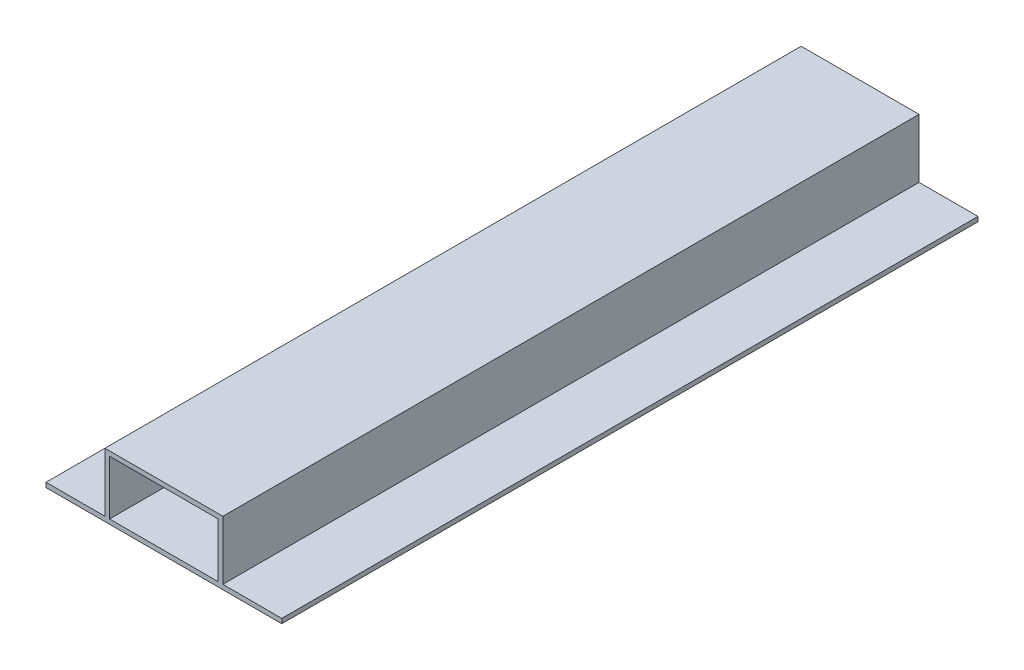
SolidWorks part; units mm, degrees
ref_plane "Alzado" through (0, 0, 0) normal (0, 0, 1) x (1, 0, 0)
ref_plane "Planta" through (0, 0, 0) normal (0, 1, 0) x (1, 0, 0)
ref_plane "Vista lateral" through (0, 0, 0) normal (1, 0, 0) x (0, 0, -1)
sketch "Croquis1" plane through (0, 0, 0) normal (0, 0, 1) x (1, 0, 0)
  line L0 (0, 31.0221) -> (0, -31.113) construction
  line L1 (38.9974, 0) -> (-46.5113, 0) construction
  line L2 (0, 12.7) -> (-11.7, 12.7)
  line L3 (0, 13.7) -> (-12.7, 13.7)
  line L4 (0, 13.7) -> (0, 1) construction
  line L5 (11.7, 1) -> (-11.7, 1)
  line L6 (-12.7, 13.7) -> (-12.7, 1)
  line L7 (25.4, 0) -> (-25.4, 0)
  line L8 (0, 0) -> (0, 1) construction
  line L9 (11.7, 1) -> (-11.7, 1)
  line L10 (-25.4, 0) -> (-25.4, 1)
  line L11 (-11.7, 12.7) -> (-11.7, 1)
  line L12 (-12.7, 1) -> (-25.4, 1)
  line L13 (12.7, 1) -> (25.4, 1)
  line L14 (11.7, 12.7) -> (11.7, 1)
  line L15 (25.4, 0) -> (25.4, 1)
  line L16 (12.7, 13.7) -> (12.7, 1)
  line L17 (0, 13.7) -> (12.7, 13.7)
  line L18 (0, 12.7) -> (11.7, 12.7)
  dimension "D1" = 12.7
  dimension "D2" = 12.7
  dimension "D3" = 1
  dimension "D4" = 1
  dimension "D5" = 25.4
extrude "Saliente-Extruir1" add sketch "Croquis1" along normal mid plane 150 contours L17 L3 L6 L12 L10 L7 L15 L13 L16 L2 L18 L14 L5 L11
